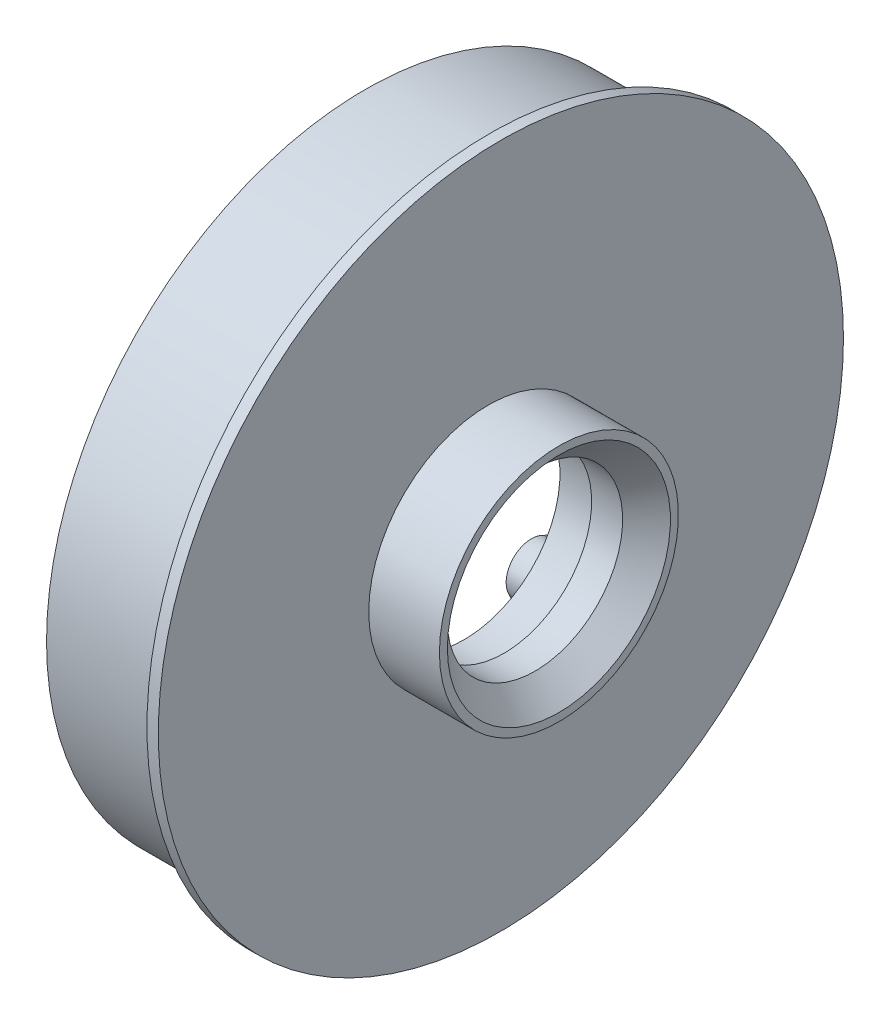
SolidWorks part; units mm, degrees
ref_plane "Front Plane" through (0, 0, 0) normal (0, 0, 1) x (1, 0, 0)
ref_plane "Top Plane" through (0, 0, 0) normal (0, 1, 0) x (1, 0, 0)
ref_plane "Right Plane" through (0, 0, 0) normal (1, 0, 0) x (0, 0, -1)
sketch "Sketch2" plane through (0, 0, 0) normal (0, 0, 1) x (1, 0, 0)
  line L0 (0, 0) -> (58.591, 0) construction
  line L2 (0, 0) -> (18.4, 0)
  line L3 (0, 0) -> (0, 2.5)
  line L4 (0, 2.5) -> (18.4, 2.5)
  line L5 (18.4, 0) -> (18.4, 2.5)
  line L6 (6.0094, 2.5) -> (6.0094, 6)
  line L11 (6.0094, 6) -> (9.9794, 6)
  line L16 (12.9794, 6) -> (12.9794, 3)
  line L17 (12.9794, 3) -> (13.6398, 3)
  line L18 (13.6398, 3) -> (13.6398, 2.5)
  line L19 (13.6398, 2.5) -> (6.0094, 2.5)
  line L22 (13.6398, 2.5) -> (16.1198, 2.5)
  line L23 (13.6398, 2.5) -> (13.6398, 4)
  line L24 (13.6398, 4) -> (16.1198, 4)
  line L25 (16.1198, 2.5) -> (16.1198, 4)
  line L27 (6.0094, 6) -> (9.9794, 6)
  line L28 (6.0094, 6) -> (6.0094, 9)
  line L29 (6.0094, 9) -> (9.9794, 9)
  line L30 (9.9794, 6) -> (9.9794, 9)
  line L31 (6.0094, 9) -> (6.0094, 8.25)
  line L32 (6.0094, 8.25) -> (5.0094, 8.25)
  line L33 (8.6609, 22.001) -> (8.6609, 12.476) construction
  line L34 (5.0094, 12.476) -> (12.3124, 12.476)
  line L35 (9.9794, 9) -> (12.3124, 9)
  line L36 (5.0094, 7.9375) -> (1.7709, 7.9375)
  line L37 (5.0094, 8.25) -> (5.0094, 12.476)
  line L38 (5.0094, 7.9375) -> (5.0094, 13.9365)
  line L39 (5.0094, 13.9365) -> (1.7709, 13.9365)
  line L40 (1.7709, 7.9375) -> (1.7709, 13.9365)
  line L41 (5.0094, 22.001) -> (12.3124, 22.001)
  line L42 (5.0094, 22.001) -> (5.0094, 30.1625)
  line L43 (5.0094, 30.1625) -> (12.3124, 30.1625)
  line L44 (12.3124, 22.001) -> (12.3124, 30.1625)
  line L49 (16.6398, 22.001) -> (16.6398, 7.5)
  line L51 (23.0198, 7.5) -> (23.0198, 6.5)
  line L54 (16.1198, 4) -> (13.6398, 4)
  line L56 (18.0398, 7.5) -> (23.0198, 7.5)
  line L57 (13.3124, 22.001) -> (16.6398, 22.001)
  line L58 (16.1198, 3.5) -> (20.0198, 3.5)
  line L59 (29.9098, 14) -> (26.9098, 11)
  line L60 (4.0094, 31.75) -> (18.0398, 31.75)
  line L61 (18.0398, 7.5) -> (23.0198, 7.5)
  line L62 (18.0398, 7.5) -> (18.0398, 12)
  line L63 (18.0398, 12) -> (23.0198, 12)
  line L64 (23.0198, 7.5) -> (23.0198, 12)
  line L65 (18.0398, 31.75) -> (18.0398, 12)
  line L66 (23.0198, 11) -> (26.9098, 11)
  line L67 (34.8098, 23) -> (31.3098, 19.5)
  line L68 (35.8098, 31) -> (38.7998, 33.99)
  line L69 (29.9098, 14) -> (29.9098, 15)
  line L70 (29.9098, 15) -> (22.9398, 15)
  line L71 (22.9398, 15) -> (21.0398, 15)
  line L72 (18.0398, 7.5) -> (16.6398, 7.5)
  line L73 (21.0398, 15) -> (21.0398, 43)
  line L74 (19.6115, 40) -> (9.6516, 40)
  line L75 (9.6516, 40) -> (4.0094, 40)
  line L76 (21.0398, 43) -> (19.6115, 43)
  line L77 (22.9398, 15) -> (29.9098, 15)
  line L78 (22.9398, 15) -> (22.9398, 21)
  line L79 (22.9398, 21) -> (29.9098, 21)
  line L80 (29.9098, 15) -> (29.9098, 21)
  line L81 (9.6516, 40) -> (19.6115, 40)
  line L82 (9.6516, 40) -> (9.6516, 50)
  line L83 (9.6516, 50) -> (19.6115, 50)
  line L84 (19.6115, 40) -> (19.6115, 50)
  line L85 (4.0094, 40) -> (4.0094, 31.75)
  line L86 (12.9794, 3) -> (12.9794, 2.5)
  line L87 (31.3098, 19.5) -> (29.9098, 19.5)
  line L88 (21.4694, 63.5) -> (21.4694, 51.308)
  line L89 (21.4694, 63.5) -> (25.9398, 63.5)
  line L90 (25.9398, 63.5) -> (25.9398, 25)
  line L91 (27.8398, 25) -> (25.9398, 25)
  line L92 (9.6516, 48) -> (8.2233, 48)
  line L93 (8.2233, 48) -> (8.2233, 53.476)
  line L94 (8.2233, 53.476) -> (19.6115, 53.476)
  line L95 (19.6115, 53.476) -> (19.6115, 50)
  line L96 (13.9174, 63.001) -> (13.9174, 53.476) construction
  line L97 (8.2233, 63.001) -> (19.6115, 63.001)
  line L98 (8.2233, 63.001) -> (8.2233, 68.2625)
  line L99 (8.2233, 68.2625) -> (19.6115, 68.2625)
  line L100 (19.6115, 63.001) -> (19.6115, 68.2625)
  line L101 (12.9794, 6) -> (11.9794, 6)
  line L102 (8.2233, 44.825) -> (4.9848, 44.825)
  line L103 (8.2233, 44.825) -> (8.2233, 54.9365)
  line L104 (8.2233, 54.9365) -> (4.9848, 54.9365)
  line L106 (9.9794, 6) -> (10.8794, 6)
  line L107 (27.8398, 25) -> (34.8098, 25)
  line L108 (34.8098, 25) -> (34.8098, 23)
  line L109 (0, 0) -> (-2, 0)
  line L110 (0, 0) -> (0, 11)
  line L111 (27.8398, 25) -> (34.8098, 25)
  line L112 (27.8398, 25) -> (27.8398, 32.5)
  line L113 (27.8398, 32.5) -> (34.8098, 32.5)
  line L114 (34.8098, 25) -> (34.8098, 32.5)
  line L115 (35.8098, 31) -> (34.8098, 31)
  line L116 (27.8398, 32.5) -> (27.8398, 64.5)
  line L117 (20.5849, 74.025) -> (6.2499, 74.025)
  line L118 (6.2499, 74.025) -> (6.2499, 76.2)
  line L119 (38.7998, 47.29) -> (30.8398, 55.25)
  line L120 (0, 11) -> (-2, 11)
  line L121 (38.7998, 43.815) -> (30.8623, 43.815)
  line L123 (-4.8152, 69.85) -> (1.5348, 76.2)
  line L124 (38.7998, 47.29) -> (38.7998, 33.99)
  line L125 (-2, 0) -> (-2, 11)
  line L126 (38.7998, 37.465) -> (30.8623, 37.465)
  line L127 (30.8623, 43.815) -> (30.8623, 37.465)
  line L128 (6.0094, 2.5) -> (6.0094, 0)
  line L129 (-0.0152, 63.5) -> (-0.0152, 30)
  line L132 (4.9848, 63.5) -> (-0.0152, 63.5)
  line L136 (-1.8152, 30) -> (-11.7752, 30)
  line L138 (-13.7752, 25.4) -> (-2, 25.4)
  line L139 (-2, 25.4) -> (-2, 11.5)
  line L140 (27.8398, 64.5) -> (20.5849, 64.5)
  line L141 (-1.8152, 30) -> (-11.7752, 30)
  line L142 (-1.8152, 30) -> (-1.8152, 39)
  line L143 (-1.8152, 39) -> (-11.7752, 39)
  line L144 (-11.7752, 30) -> (-11.7752, 39)
  line L145 (20.5849, 64.5) -> (20.5849, 74.025)
  line L146 (-12.7752, 37) -> (-12.7752, 47.29)
  line L147 (-12.7752, 37) -> (-11.7752, 37)
  line L148 (30.8398, 55.25) -> (30.8398, 76.2)
  line L149 (11.9794, 6) -> (11.9794, 5.45)
  line L154 (-2, 11.5) -> (0.5, 11.5)
  line L155 (4.9848, 60.6197) -> (24.0348, 60.6197)
  line L160 (4.9848, 60.6197) -> (4.9848, 55.8572)
  line L161 (4.9848, 55.8572) -> (24.0348, 55.8572)
  line L166 (24.0348, 60.6197) -> (24.0348, 55.8572)
  line L167 (4.9848, 60.6197) -> (24.0348, 55.8572) construction
  line L172 (4.9848, 55.8572) -> (24.0348, 60.6197) construction
  line L173 (24.0348, 62.2072) -> (25.9398, 62.2072)
  line L174 (11.9794, 5.45) -> (10.8794, 5.45)
  line L175 (10.8794, 6) -> (10.8794, 5.45)
  line L176 (24.0348, 62.2072) -> (24.0348, 54.2697)
  line L177 (24.0348, 54.2697) -> (25.9398, 54.2697)
  line L178 (25.9398, 62.2072) -> (25.9398, 54.2697)
  line L179 (24.0348, 62.2072) -> (25.9398, 54.2697) construction
  line L180 (24.0348, 54.2697) -> (25.9398, 62.2072) construction
  line L181 (3, 19.6197) -> (15.7, 19.6197)
  line L182 (3, 19.6197) -> (3, 14.8572)
  line L183 (3, 14.8572) -> (15.7, 14.8572)
  line L184 (15.7, 19.6197) -> (15.7, 14.8572)
  line L185 (3, 19.6197) -> (15.7, 14.8572) construction
  line L186 (3, 14.8572) -> (15.7, 19.6197) construction
  line L187 (15.7, 21.2072) -> (16.6398, 21.2072)
  line L188 (15.7, 21.2072) -> (15.7, 13.2697)
  line L189 (15.7, 13.2697) -> (16.6398, 13.2697)
  line L190 (16.6398, 21.2072) -> (16.6398, 13.2697)
  line L191 (15.7, 21.2072) -> (16.6398, 13.2697) construction
  line L192 (15.7, 13.2697) -> (16.6398, 21.2072) construction
  line L193 (0.5, 11.5) -> (0.5, 6.9375)
  line L194 (0.5, 6.9375) -> (1.7709, 6.9375)
  line L195 (23.0198, 6.5) -> (20.0198, 3.5)
  line L196 (4.9848, 63.5) -> (4.9848, 54.9365)
  line L197 (3, 43.825) -> (4.9848, 43.825)
  line L198 (1.7709, 6.9375) -> (1.7709, 7.9375)
  line L199 (6.0094, 0) -> (12.9794, 0)
  line L200 (12.9794, 0) -> (12.9794, 2.5)
  line L201 (18.0398, 31.75) -> (18.0398, 35.875)
  line L202 (18.0398, 35.875) -> (21.0398, 35.875)
  line L203 (30.8398, 76.2) -> (6.2499, 76.2)
  line L204 (2.8049, 69.85) -> (7.2499, 69.85) construction
  line L205 (7.2499, 67.4688) -> (26.2999, 67.4688)
  line L206 (7.2499, 74.025) -> (7.2499, 64.5)
  line L207 (7.2499, 64.5) -> (-1.8152, 64.5)
  line L208 (-1.8152, 64.5) -> (-1.8152, 39)
  line L209 (-12.7752, 47.29) -> (-4.8152, 55.25)
  line L210 (-4.8152, 55.25) -> (-4.8152, 69.85)
  line L211 (7.2499, 67.4688) -> (7.2499, 72.2312)
  line L212 (7.2499, 72.2312) -> (26.2999, 72.2313)
  line L213 (26.2999, 67.4688) -> (26.2999, 72.2313)
  line L214 (26.2999, 73.8187) -> (30.8398, 73.8187)
  line L215 (26.2999, 73.8187) -> (26.2999, 65.8813)
  line L216 (26.2999, 65.8813) -> (30.8398, 65.8813)
  line L217 (30.8398, 73.8187) -> (30.8398, 65.8813)
  line L218 (2.8049, 72.2313) -> (25.0299, 72.2313)
  line L219 (2.8049, 72.2313) -> (2.8049, 67.4687)
  line L220 (2.8049, 67.4687) -> (25.0299, 67.4687)
  line L221 (25.0299, 72.2313) -> (25.0299, 67.4687)
  line L222 (25.0299, 69.85) -> (20.5849, 69.85) construction
  line L223 (21.4694, 51.308) -> (22.9398, 51.308)
  line L224 (22.9398, 51.308) -> (22.9398, 21)
  line L225 (13.6398, 4) -> (13.6398, 12.2697)
  line L226 (13.6398, 12.2697) -> (13.3124, 12.2697)
  line L227 (13.3124, 12.2697) -> (13.3124, 22.001)
  line L228 (12.3124, 9) -> (12.3124, 12.476)
  line L229 (-1.8152, 30) -> (-0.0152, 30)
  line L230 (8.2233, 65.6317) -> (2.8049, 65.6317) construction
  line L231 (19.6115, 65.6317) -> (25.0299, 65.6317) construction
  line L232 (1.5348, 76.2) -> (6.2499, 76.2)
  line L233 (-11.7752, 30) -> (-13.7752, 30)
  line L234 (-13.7752, 30) -> (-13.7752, 25.4)
  line L235 (3, 13.9365) -> (3, 43.825)
  line L236 (4.9848, 54.9365) -> (4.9848, 44.825)
  line L237 (4.9848, 43.825) -> (4.9848, 44.825)
  circle A0 centre (26.8898, 25.95) radius 0.95
  circle A1 centre (21.9898, 15.95) radius 0.95
  circle A2 centre (17.3398, 8.2) radius 0.7
  circle A3 centre (10.4294, 6.45) radius 0.45
  circle A4 centre (-0.9152, 30.9) radius 0.9
  point P7 (24.9873, 58.2385)
  point P131 (16.1699, 17.2385)
  point P135 (14.5098, 58.2385)
  point P146 (9.35, 17.2385)
sketch "Sketch3" plane through (0, 0, 0) normal (1, 0, 0) x (0, 0, -1)
  line L0 (0, 0) -> (0, 69.85) construction
  line L1 (0, 0) -> (13.6271, 68.5079) construction
  line L2 (0, 0) -> (0, 58.2385) construction
  line L3 (0, 0) -> (50.436, 29.1192) construction
  line L4 (0, 0) -> (0, 31.75) construction
  line L5 (0, 0) -> (12.1502, 29.3332) construction
  line L6 (0, 0) -> (0, 17.2385) construction
  line L7 (0, 0) -> (14.929, 8.6192) construction
  line L8 (0, 0) -> (0, 58.2385) construction
  line L9 (0, 0) -> (50.436, 29.1192) construction
  line L10 (0, 0) -> (5.9583, 29.9542) construction
  line L11 (0, 0) -> (16.9677, 25.394) construction
  circle A0 centre (0, 0) radius 69.85 construction
  circle A1 centre (0, 0) radius 58.2385 construction
  circle A2 centre (0, 0) radius 31.75 construction
  circle A3 centre (0, 0) radius 17.2385 construction
  circle A4 centre (0, 69.85) radius 3.175
  circle A5 centre (0, 58.2385) radius 4.7625
  circle A6 centre (0, 31.75) radius 3.175
  circle A7 centre (0, 17.2385) radius 4.7625
  circle A8 centre (13.6271, 68.5079) radius 3.175
  circle A9 centre (26.7304, 64.533) radius 3.175
  circle A10 centre (38.8066, 58.0782) radius 3.175
  circle A11 centre (49.3914, 49.3914) radius 3.175
  circle A12 centre (58.0782, 38.8066) radius 3.175
  circle A13 centre (64.533, 26.7304) radius 3.175
  circle A14 centre (68.5079, 13.6271) radius 3.175
  circle A15 centre (69.85, 0) radius 3.175
  circle A16 centre (68.5079, -13.6271) radius 3.175
  circle A17 centre (64.533, -26.7304) radius 3.175
  circle A18 centre (58.0782, -38.8066) radius 3.175
  circle A19 centre (49.3914, -49.3914) radius 3.175
  circle A20 centre (38.8066, -58.0782) radius 3.175
  circle A21 centre (26.7304, -64.533) radius 3.175
  circle A22 centre (13.6271, -68.5079) radius 3.175
  circle A23 centre (0, -69.85) radius 3.175
  circle A24 centre (-13.6271, -68.5079) radius 3.175
  circle A25 centre (-26.7304, -64.533) radius 3.175
  circle A26 centre (-38.8066, -58.0782) radius 3.175
  circle A27 centre (-49.3914, -49.3914) radius 3.175
  circle A28 centre (-58.0782, -38.8066) radius 3.175
  circle A29 centre (-64.533, -26.7304) radius 3.175
  circle A30 centre (-68.5079, -13.6271) radius 3.175
  circle A31 centre (-69.85, 0) radius 3.175
  circle A32 centre (-68.5079, 13.6271) radius 3.175
  circle A33 centre (-64.533, 26.7304) radius 3.175
  circle A34 centre (-58.0782, 38.8066) radius 3.175
  circle A35 centre (-49.3914, 49.3914) radius 3.175
  circle A36 centre (-38.8066, 58.0782) radius 3.175
  circle A37 centre (-26.7304, 64.533) radius 3.175
  circle A38 centre (-13.6271, 68.5079) radius 3.175
  circle A47 centre (50.436, 29.1192) radius 4.7625
  circle A48 centre (50.436, -29.1192) radius 4.7625
  circle A49 centre (0, -58.2385) radius 4.7625
  circle A50 centre (-50.436, -29.1192) radius 4.7625
  circle A51 centre (-50.436, 29.1192) radius 4.7625
  circle A58 centre (12.1502, 29.3332) radius 3.175
  circle A59 centre (22.4506, 22.4506) radius 3.175
  circle A60 centre (29.3332, 12.1502) radius 3.175
  circle A61 centre (31.75, 0) radius 3.175
  circle A62 centre (29.3332, -12.1502) radius 3.175
  circle A63 centre (22.4506, -22.4506) radius 3.175
  circle A64 centre (12.1502, -29.3332) radius 3.175
  circle A65 centre (0, -31.75) radius 3.175
  circle A66 centre (-12.1502, -29.3332) radius 3.175
  circle A67 centre (-22.4506, -22.4506) radius 3.175
  circle A68 centre (-29.3332, -12.1502) radius 3.175
  circle A69 centre (-31.75, 0) radius 3.175
  circle A70 centre (-29.3332, 12.1502) radius 3.175
  circle A71 centre (-22.4506, 22.4506) radius 3.175
  circle A72 centre (14.929, 8.6192) radius 4.7625
  circle A73 centre (14.929, -8.6192) radius 4.7625
  circle A74 centre (0, -17.2385) radius 4.7625
  circle A75 centre (-14.929, -8.6192) radius 4.7625
  circle A76 centre (-14.929, 8.6192) radius 4.7625
  circle A77 centre (0, 0) radius 50
  circle A78 centre (0, 0) radius 9
  circle A79 centre (-12.1502, 29.3332) radius 3.175
  circle A80 centre (0, 0) radius 76.2
  circle A81 centre (0, 0) radius 74.025
  circle A82 centre (0, 69.85) radius 3.9687
  circle A83 centre (49.3914, 49.3914) radius 3.9687
  circle A84 centre (69.85, 0) radius 3.9688
  circle A85 centre (49.3914, -49.3914) radius 3.9687
  circle A86 centre (0, -69.85) radius 3.9687
  circle A87 centre (-49.3914, -49.3914) radius 3.9687
  circle A88 centre (-69.85, 0) radius 3.9688
  circle A89 centre (-49.3914, 49.3914) radius 3.9687
  circle A90 centre (0, 69.85) radius 2.3812
  circle A91 centre (13.6271, 68.5079) radius 2.3812
  circle A92 centre (26.7304, 64.533) radius 2.3813
  circle A93 centre (38.8066, 58.0782) radius 2.3812
  circle A94 centre (49.3914, 49.3914) radius 2.3812
  circle A95 centre (58.0782, 38.8066) radius 2.3812
  circle A96 centre (64.533, 26.7304) radius 2.3813
  circle A97 centre (68.5079, 13.6271) radius 2.3813
  circle A98 centre (69.85, 0) radius 2.3813
  circle A99 centre (68.5079, -13.6271) radius 2.3813
  circle A100 centre (64.533, -26.7304) radius 2.3813
  circle A101 centre (58.0782, -38.8066) radius 2.3812
  circle A102 centre (49.3914, -49.3914) radius 2.3812
  circle A103 centre (38.8066, -58.0782) radius 2.3812
  circle A104 centre (26.7304, -64.533) radius 2.3813
  circle A105 centre (13.6271, -68.5079) radius 2.3812
  circle A106 centre (0, -69.85) radius 2.3812
  circle A107 centre (-13.6271, -68.5079) radius 2.3812
  circle A108 centre (-26.7304, -64.533) radius 2.3813
  circle A109 centre (-38.8066, -58.0782) radius 2.3812
  circle A110 centre (-49.3914, -49.3914) radius 2.3812
  circle A111 centre (-58.0782, -38.8066) radius 2.3812
  circle A112 centre (-64.533, -26.7304) radius 2.3812
  arc A113 (3.0399, 30.8338) -> (8.9911, 29.65) centre (5.9583, 29.9542) cw
  arc A114 (14.6081, 27.3234) -> (19.6532, 23.9523) centre (16.9677, 25.394) cw
  arc A115 (23.9523, 19.6532) -> (27.3234, 14.6081) centre (25.394, 16.9677) cw
  arc A116 (29.65, 8.9911) -> (30.8338, 3.0399) centre (29.9542, 5.9583) cw
  arc A117 (30.8338, -3.0399) -> (29.65, -8.9911) centre (29.9542, -5.9583) cw
  arc A118 (27.3234, -14.6081) -> (23.9523, -19.6532) centre (25.394, -16.9677) cw
  arc A119 (19.6532, -23.9523) -> (14.6081, -27.3234) centre (16.9677, -25.394) cw
  arc A120 (8.9911, -29.65) -> (3.0399, -30.8338) centre (5.9583, -29.9542) cw
  arc A121 (-3.0399, -30.8338) -> (-8.9911, -29.65) centre (-5.9583, -29.9542) cw
  arc A122 (-14.6081, -27.3234) -> (-19.6532, -23.9523) centre (-16.9677, -25.394) cw
  arc A123 (-23.9523, -19.6532) -> (-27.3234, -14.6081) centre (-25.394, -16.9677) cw
  arc A124 (-29.65, -8.9911) -> (-30.8338, -3.0399) centre (-29.9542, -5.9583) cw
  arc A125 (-30.8338, 3.0399) -> (-29.65, 8.9911) centre (-29.9542, 5.9583) cw
  arc A126 (-27.3234, 14.6081) -> (-23.9523, 19.6532) centre (-25.394, 16.9677) cw
  arc A127 (-19.6532, 23.9523) -> (-14.6081, 27.3234) centre (-16.9677, 25.394) cw
  arc A128 (-8.9911, 29.65) -> (-3.0399, 30.8338) centre (-5.9583, 29.9542) cw
  arc A129 (26.9875, 0) -> (26.9932, 0.1932) centre (30.2705, 0) cw
  arc A130 (65.0988, 0.2771) -> (65.0875, 0) centre (68.4964, 0) ccw
  circle A131 centre (1.5875, 0) radius 40
  circle A132 centre (1.5875, 0) radius 2.5
  circle A133 centre (1.5875, 0) radius 3
  circle A134 centre (1.5875, 0) radius 43
  circle A135 centre (-68.5079, -13.6271) radius 2.3813
  circle A136 centre (-69.85, 0) radius 2.3813
  circle A137 centre (-68.5079, 13.6271) radius 2.3813
  circle A138 centre (-64.533, 26.7304) radius 2.3812
  circle A139 centre (-58.0782, 38.8066) radius 2.3812
  circle A140 centre (-49.3914, 49.3914) radius 2.3812
  circle A141 centre (-38.8066, 58.0782) radius 2.3812
  circle A142 centre (-26.7304, 64.533) radius 2.3813
  circle A143 centre (-13.6271, 68.5079) radius 2.3812
  circle A144 centre (0, 58.2385) radius 2.3812
  circle A145 centre (0, 58.2385) radius 3.9688
  circle A146 centre (50.436, 29.1192) radius 3.9688
  circle A147 centre (50.436, 29.1192) radius 2.3813
  circle A148 centre (50.436, -29.1192) radius 3.9687
  circle A149 centre (50.436, -29.1192) radius 2.3812
  circle A150 centre (0, -58.2385) radius 3.9687
  circle A151 centre (0, -58.2385) radius 2.3812
  circle A152 centre (-50.436, -29.1192) radius 3.9687
  circle A153 centre (-50.436, -29.1192) radius 2.3812
  circle A154 centre (-50.436, 29.1192) radius 3.9687
  circle A155 centre (-50.436, 29.1192) radius 2.3812
  spline S1 degree 4 number of poles 499 (26.9875, 0) -> (26.9932, 0.1932)
  spline S3 degree 4 number of poles 617 (65.0875, 0) -> (65.0988, 0.2771)
  point P116 (0, 0)
  point P225 (0, 0)
sketch "Sketch5" plane through (0, 0, 0) normal (0, 0, 1) x (1, 0, 0)
  line L0 (23.0198, 7.5) -> (23.0198, 12) construction
  line L2 (22.9398, 15) -> (21.0398, 15) construction
  line L3 (29.9098, 14) -> (29.9098, 15) construction
  line L4 (29.9098, 15) -> (22.9398, 15) construction
  line L5 (29.9098, 14) -> (26.9098, 11) construction
  line L6 (23.0198, 11) -> (26.9098, 11) construction
  line L7 (18.0398, 12) -> (23.0198, 12) construction
  line L8 (18.0398, 31.75) -> (18.0398, 12) construction
  line L10 (18.0398, 35.875) -> (21.0398, 35.875) construction
  line L11 (18.0398, 31.75) -> (18.0398, 35.875) construction
  line L12 (23.0198, 11) -> (23.0198, 12)
  line L14 (22.9398, 15) -> (21.0398, 15)
  line L15 (29.9098, 14) -> (29.9098, 15)
  line L16 (29.9098, 15) -> (22.9398, 15)
  line L17 (29.9098, 14) -> (26.9098, 11)
  line L18 (23.0198, 11) -> (26.9098, 11)
  line L19 (18.0398, 12) -> (23.0198, 12)
  line L20 (18.0398, 31.75) -> (18.0398, 12)
  line L22 (18.0398, 35.875) -> (21.0398, 35.875)
  line L23 (18.0398, 31.75) -> (18.0398, 35.875)
  line L24 (21.0398, 15) -> (21.0398, 43) construction
  line L25 (21.0398, 15) -> (21.0398, 35.875)
revolve "Revolve1" add sketch "Sketch5" angle 360 about L0
sketch "Sketch6" plane through (0, 0, 0) normal (1, 0, 0) x (0, 0, -1)
  arc A0 (19.6532, 23.9523) -> (14.6081, 27.3234) centre (16.9677, 25.394) ccw construction
  circle A1 centre (12.1502, 29.3332) radius 3.175 construction
  arc A2 (8.9911, 29.65) -> (3.0399, 30.8338) centre (5.9583, 29.9542) ccw construction
  circle A3 centre (0, 31.75) radius 3.175 construction
  arc A4 (-3.0399, 30.8338) -> (-8.9911, 29.65) centre (-5.9583, 29.9542) ccw construction
  circle A5 centre (22.4506, 22.4506) radius 3.175 construction
  arc A6 (27.3234, 14.6081) -> (23.9523, 19.6532) centre (25.394, 16.9677) ccw construction
  circle A7 centre (29.3332, 12.1502) radius 3.175 construction
  arc A8 (30.8338, 3.0399) -> (29.65, 8.9911) centre (29.9542, 5.9583) ccw construction
  circle A9 centre (31.75, 0) radius 3.175 construction
  arc A10 (29.65, -8.9911) -> (30.8338, -3.0399) centre (29.9542, -5.9583) ccw construction
  circle A11 centre (29.3332, -12.1502) radius 3.175 construction
  arc A12 (23.9523, -19.6532) -> (27.3234, -14.6081) centre (25.394, -16.9677) ccw construction
  circle A13 centre (22.4506, -22.4506) radius 3.175 construction
  arc A14 (14.6081, -27.3234) -> (19.6532, -23.9523) centre (16.9677, -25.394) ccw construction
  circle A15 centre (12.1502, -29.3332) radius 3.175 construction
  arc A16 (3.0399, -30.8338) -> (8.9911, -29.65) centre (5.9583, -29.9542) ccw construction
  circle A17 centre (0, -31.75) radius 3.175 construction
  arc A18 (-8.9911, -29.65) -> (-3.0399, -30.8338) centre (-5.9583, -29.9542) ccw construction
  circle A19 centre (-12.1502, -29.3332) radius 3.175 construction
  arc A20 (-19.6532, -23.9523) -> (-14.6081, -27.3234) centre (-16.9677, -25.394) ccw construction
  circle A21 centre (-22.4506, -22.4506) radius 3.175 construction
  arc A22 (-27.3234, -14.6081) -> (-23.9523, -19.6532) centre (-25.394, -16.9677) ccw construction
  circle A23 centre (-29.3332, -12.1502) radius 3.175 construction
  arc A24 (-30.8338, -3.0399) -> (-29.65, -8.9911) centre (-29.9542, -5.9583) ccw construction
  circle A25 centre (-31.75, 0) radius 3.175 construction
  arc A26 (-29.65, 8.9911) -> (-30.8338, 3.0399) centre (-29.9542, 5.9583) ccw construction
  circle A27 centre (-29.3332, 12.1502) radius 3.175 construction
  arc A28 (-23.9523, 19.6532) -> (-27.3234, 14.6081) centre (-25.394, 16.9677) ccw construction
  circle A29 centre (-12.1502, 29.3332) radius 3.175 construction
  arc A30 (-14.6081, 27.3234) -> (-19.6532, 23.9523) centre (-16.9677, 25.394) ccw construction
  circle A31 centre (-22.4506, 22.4506) radius 3.175 construction
  circle A32 centre (1.5875, 0) radius 43 construction
  arc A33 (19.6532, 23.9523) -> (14.6081, 27.3234) centre (16.9677, 25.394) ccw
  arc A34 (8.9911, 29.65) -> (14.6081, 27.3234) centre (12.1502, 29.3332) ccw
  arc A35 (8.9911, 29.65) -> (3.0399, 30.8338) centre (5.9583, 29.9542) ccw
  arc A36 (-3.0399, 30.8338) -> (3.0399, 30.8338) centre (0, 31.75) ccw
  arc A37 (-3.0399, 30.8338) -> (-8.9911, 29.65) centre (-5.9583, 29.9542) ccw
  arc A38 (19.6532, 23.9523) -> (23.9523, 19.6532) centre (22.4506, 22.4506) ccw
  arc A39 (27.3234, 14.6081) -> (23.9523, 19.6532) centre (25.394, 16.9677) ccw
  arc A40 (27.3234, 14.6081) -> (29.65, 8.9911) centre (29.3332, 12.1502) ccw
  arc A41 (30.8338, 3.0399) -> (29.65, 8.9911) centre (29.9542, 5.9583) ccw
  arc A42 (30.8338, 3.0399) -> (30.8338, -3.0399) centre (31.75, 0) ccw
  arc A43 (29.65, -8.9911) -> (30.8338, -3.0399) centre (29.9542, -5.9583) ccw
  arc A44 (29.65, -8.9911) -> (27.3234, -14.6081) centre (29.3332, -12.1502) ccw
  arc A45 (23.9523, -19.6532) -> (27.3234, -14.6081) centre (25.394, -16.9677) ccw
  arc A46 (23.9523, -19.6532) -> (19.6532, -23.9523) centre (22.4506, -22.4506) ccw
  arc A47 (14.6081, -27.3234) -> (19.6532, -23.9523) centre (16.9677, -25.394) ccw
  arc A48 (14.6081, -27.3234) -> (8.9911, -29.65) centre (12.1502, -29.3332) ccw
  arc A49 (3.0399, -30.8338) -> (8.9911, -29.65) centre (5.9583, -29.9542) ccw
  arc A50 (3.0399, -30.8338) -> (-3.0399, -30.8338) centre (0, -31.75) ccw
  arc A51 (-8.9911, -29.65) -> (-3.0399, -30.8338) centre (-5.9583, -29.9542) ccw
  arc A52 (-8.9911, -29.65) -> (-14.6081, -27.3234) centre (-12.1502, -29.3332) ccw
  arc A53 (-19.6532, -23.9523) -> (-14.6081, -27.3234) centre (-16.9677, -25.394) ccw
  arc A54 (-19.6532, -23.9523) -> (-23.9523, -19.6532) centre (-22.4506, -22.4506) ccw
  arc A55 (-27.3234, -14.6081) -> (-23.9523, -19.6532) centre (-25.394, -16.9677) ccw
  arc A56 (-27.3234, -14.6081) -> (-29.65, -8.9911) centre (-29.3332, -12.1502) ccw
  arc A57 (-30.8338, -3.0399) -> (-29.65, -8.9911) centre (-29.9542, -5.9583) ccw
  arc A58 (-30.8338, -3.0399) -> (-30.8338, 3.0399) centre (-31.75, 0) ccw
  arc A59 (-29.65, 8.9911) -> (-30.8338, 3.0399) centre (-29.9542, 5.9583) ccw
  arc A60 (-29.65, 8.9911) -> (-27.3234, 14.6081) centre (-29.3332, 12.1502) ccw
  arc A61 (-23.9523, 19.6532) -> (-27.3234, 14.6081) centre (-25.394, 16.9677) ccw
  arc A62 (-14.6081, 27.3234) -> (-8.9911, 29.65) centre (-12.1502, 29.3332) ccw
  arc A63 (-14.6081, 27.3234) -> (-19.6532, 23.9523) centre (-16.9677, 25.394) ccw
  arc A64 (-23.9523, 19.6532) -> (-19.6532, 23.9523) centre (-22.4506, 22.4506) ccw
  circle A65 centre (1.5875, 0) radius 43
extrude "Boss-Extrude1" add sketch "Sketch6" along normal up to vertex from vertex contours A65 A61 A64 A63 A62 A37 A36 A35 A34 A33 A38 A39 A40 A41 A42 A43 A44 A45 A46 A47 A48 A49 A50 A51 A52 A53 A54 A55 A56 A57 A58 A59 A60
sketch "Sketch7" plane through (0, 0, 0) normal (1, 0, 0) x (0, 0, -1)
  circle A0 centre (1.5875, 0) radius 43 construction
  circle A1 centre (1.5875, 0) radius 40 construction
  circle A2 centre (1.5875, 0) radius 43
  circle A3 centre (1.5875, 0) radius 40
extrude "Cut-Extrude1" cut sketch "Sketch7" along normal up to vertex
